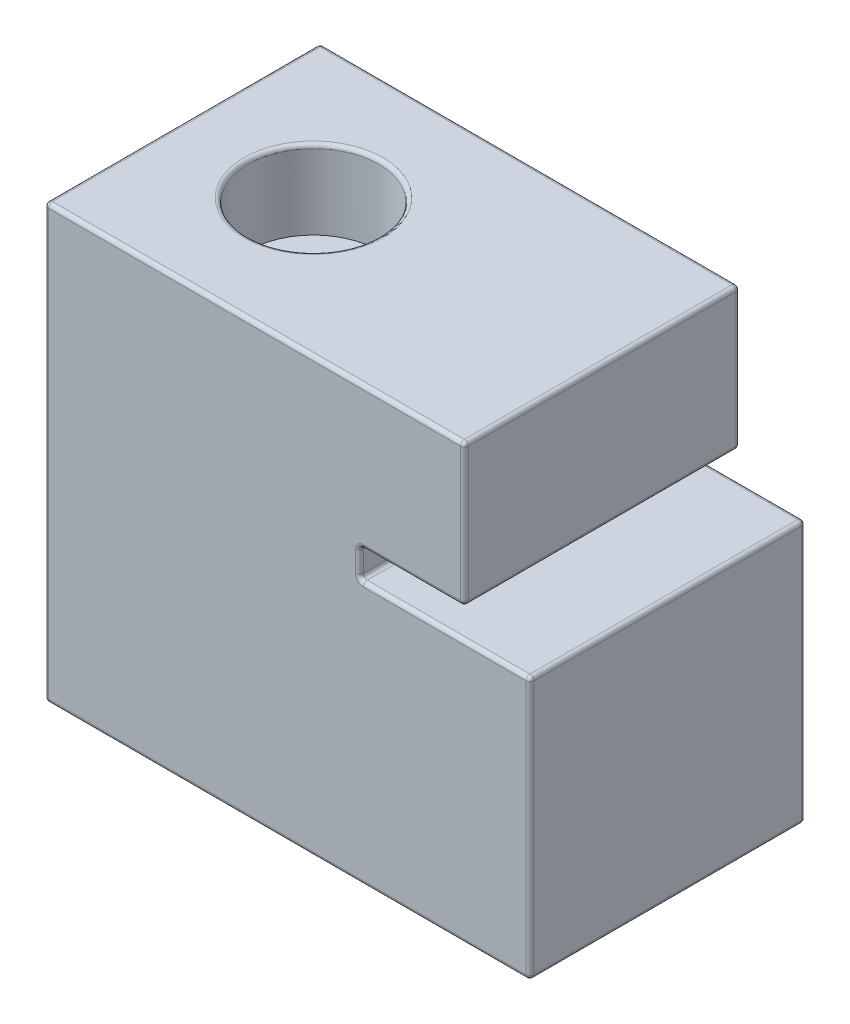
SolidWorks part; units mm, degrees
ref_plane "Front Plane" through (0, 0, 0) normal (0, 0, 1) x (1, 0, 0)
ref_plane "Top Plane" through (0, 0, 0) normal (0, 1, 0) x (1, 0, 0)
ref_plane "Right Plane" through (0, 0, 0) normal (1, 0, 0) x (0, 0, -1)
sketch "Sketch1" plane through (0, 0, 0) normal (0, 0, 1) x (1, 0, 0)
  line L0 (32, 33) -> (32, 22.2)
  line L1 (0, 0) -> (37, 0)
  line L2 (0, 0) -> (0, 33)
  line L3 (0, 33) -> (32, 33)
  line L4 (37, 0) -> (37, 20)
  line L5 (32, 22.2) -> (24, 22.2)
  line L6 (24, 22.2) -> (24, 20)
  line L7 (24, 20) -> (37, 20)
  dimension "D1" = 37
  dimension "D2" = 33
  dimension "D3" = 32
  dimension "D4" = 2.2
  dimension "D5" = 20
  dimension "D6" = 8
extrude "Boss-Extrude1" add sketch "Sketch1" along normal blind 21
sketch "Sketch2" plane through (0, 33, 0) normal (0, 1, 0) x (1, 0, 0)
  line L0 (0, -21) -> (0, 0) construction
  circle A0 centre (10, -10.5) radius 2.65
  dimension "D1" = 5.3
  dimension "D2" = 10.5
  dimension "D3" = 10
extrude "Cut-Extrude1" cut sketch "Sketch2" against normal through all
sketch "Sketch3" plane through (0, 33, 0) normal (0, 1, 0) x (1, 0, 0)
  circle A0 centre (10, -10.5) radius 5
  dimension "D1" = 10
extrude "Cut-Extrude2" cut sketch "Sketch3" against normal blind 6
fillet "Fillet1" radius 0.3 26 edges at (10, 33, 15.5) (24, 20, 10.5) (24, 22.2, 10.5) (32, 22.2, 10.5) (32, 33, 10.5) (37, 20, 10.5) (37, 0, 10.5) (10, 0, 13.15) (18.5, 0, 0) (37, 10, 0) (30.5, 20, 0) (24, 21.1, 0) (28, 22.2, 0) (32, 27.6, 0) (16, 33, 0) (0, 33, 10.5) (0, 0, 10.5) (0, 16.5, 0) (16, 33, 21) (32, 27.6, 21) (28, 22.2, 21) (24, 21.1, 21) (30.5, 20, 21) (37, 10, 21) (18.5, 0, 21) (0, 16.5, 21)
